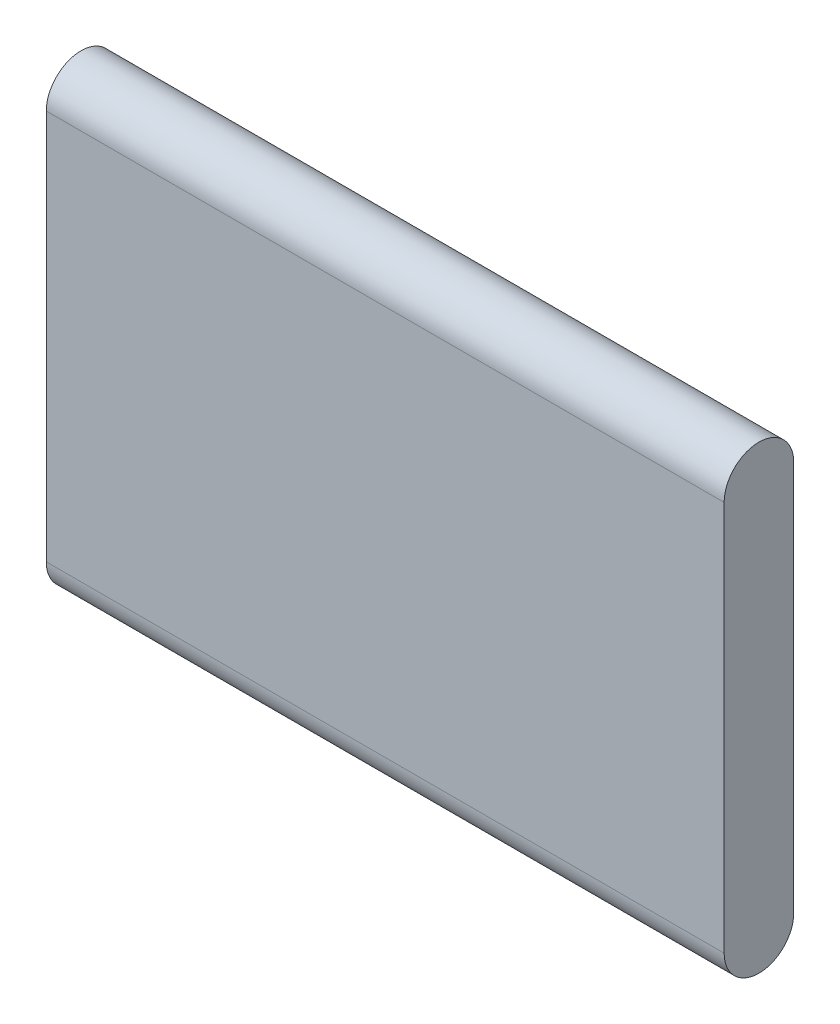
SolidWorks part; units mm, degrees
ref_plane "Front Plane" through (0, 0, 0) normal (0, 0, 1) x (1, 0, 0)
ref_plane "Top Plane" through (0, 0, 0) normal (0, 1, 0) x (1, 0, 0)
ref_plane "Right Plane" through (0, 0, 0) normal (1, 0, 0) x (0, 0, -1)
sketch "Sketch1" plane through (0, 0, 0) normal (1, 0, 0) x (0, 0, -1)
  line L0 (-36.5125, 204.7875) -> (36.5125, -204.7875) construction
  line L2 (-36.5125, 204.7875) -> (-36.5125, -204.7875)
  line L4 (36.5125, 204.7875) -> (36.5125, -204.7875)
  arc A0 (36.5125, 204.7875) -> (-36.5125, 204.7875) centre (0, 204.7875) ccw
  arc A1 (-36.5125, -204.7875) -> (36.5125, -204.7875) centre (0, -204.7875) ccw
  dimension "D1" = 36.5125
  dimension "D2" = 482.6
extrude "Boss-Extrude1" add sketch "Sketch1" along normal mid plane 711.2
